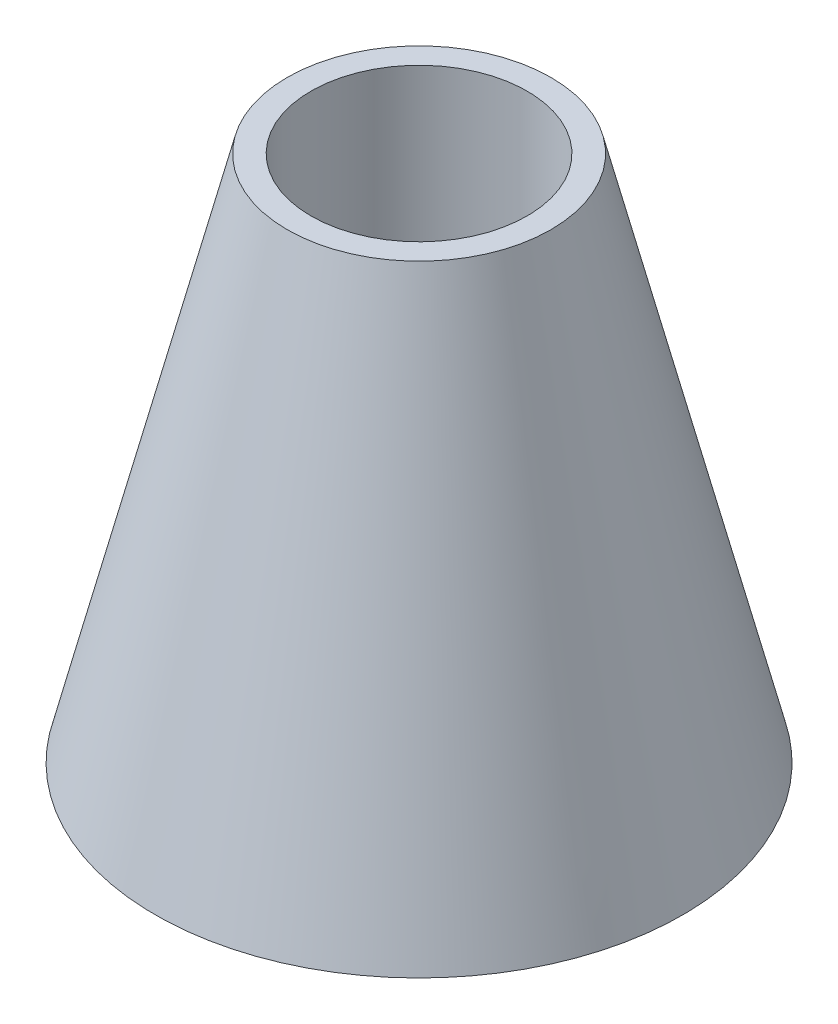
SolidWorks part; units mm, degrees
ref_plane "Front Plane" through (0, 0, 0) normal (0, 0, 1) x (1, 0, 0)
ref_plane "Top Plane" through (0, 0, 0) normal (0, 1, 0) x (1, 0, 0)
ref_plane "Right Plane" through (0, 0, 0) normal (1, 0, 0) x (0, 0, -1)
sketch "Sketch3" plane through (0, 0, 0) normal (1, 0, 0) x (0, 0, -1)
  line L0 (0, 0) -> (0, 67.6853) construction
  line L1 (0, 0) -> (0, -74.4258) construction
  line L2 (0, 0) -> (100, 0)
  line L3 (0, 0) -> (0, 200)
  line L4 (0, 200) -> (50, 200)
  line L5 (50, 200) -> (100, 0)
  point P9 (52.6579, 209.0465)
  dimension "D1" = 200
  dimension "D2" = 50
  dimension "D3" = 100
revolve "Revolve1" add sketch "Sketch3" angle 360 about L3
sketch "Sketch5" plane through (0, 0, 0) normal (0, 1, 0) x (1, 0, 0)
  circle A0 centre (0, 0) radius 41
  dimension "D1" = 82
extrude "Cut-Extrude2" cut sketch "Sketch5" along normal blind 200 contours A0
sketch "Sketch6" plane through (0, 0, 0) normal (0, -1, 0) x (1, 0, 0)
  circle A0 centre (0, 0) radius 40
  circle A1 centre (0, 0) radius 95
  point P4 (0, 0)
  dimension "D1" = 55
sketch "Sketch7" plane through (0, 0, 0) normal (1, 0, 0) x (0, 0, -1)
  line L2 (96.9231, 2) -> (48.0481, 197.5)
  line L4 (50, 200) -> (100, 0) construction
  line L10 (48.0481, 197.5) -> (42.5, 197.5)
  line L11 (42.5, 197.5) -> (42.5, 2)
  line L12 (42.5, 2) -> (96.9231, 2)
  line L13 (-41, 0) -> (41, 0) construction
  line L15 (50, 200) -> (-50, 200) construction
  dimension "D1" = 2.5
  dimension "D2" = 2
  dimension "D3" = 42.5
  dimension "D4" = 2.5
revolve "Cut-Revolve1" cut sketch "Sketch7" angle 360 about L1
sketch "Sketch10" plane through (0, 0, 0) normal (0, -1, 0) x (1, 0, 0)
  circle A8 centre (0, 0) radius 99
  circle A9 centre (0, 0) radius 42
  circle A10 centre (0, 0) radius 100 construction
  circle A11 centre (0, 0) radius 41 construction
  dimension "D1" = 1
  dimension "D2" = 1
extrude "Cut-Extrude3" cut sketch "Sketch10" against normal blind 2.1 and the other way through all
sketch "Sketch11" plane through (0, 0, 0) normal (1, 0, 0) x (0, 0, -1)
  line L0 (41, 200) -> (41, 5.0912) construction
